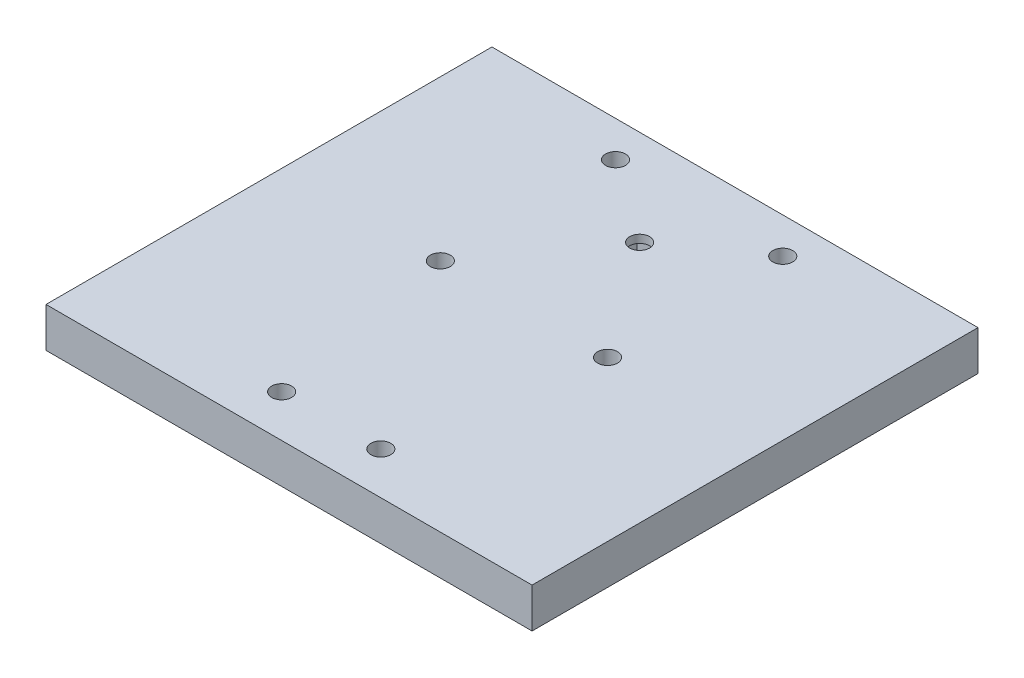
SolidWorks part; units mm, degrees
ref_plane "Front Plane" through (0, 0, 0) normal (0, 0, 1) x (1, 0, 0)
ref_plane "Top Plane" through (0, 0, 0) normal (0, 1, 0) x (1, 0, 0)
ref_plane "Right Plane" through (0, 0, 0) normal (1, 0, 0) x (0, 0, -1)
sketch "Sketch2" plane through (0, 0, 0) normal (0, 1, 0) x (1, 0, 0)
  line L1 (61.04, -67.5) -> (-61.04, -67.5)
  line L2 (61.04, -67.5) -> (61.04, 37.5)
  line L4 (-61.04, -67.5) -> (-61.04, 37.5)
  line L7 (-61.04, 37.5) -> (-61.04, 44.5)
  line L8 (-61.04, 44.5) -> (61.04, 44.5)
  line L9 (61.04, 44.5) -> (61.04, 37.5)
  point P0 (0, 0)
  dimension "D1" = 112
  dimension "D4" = 122.08
extrude "Boss-Extrude1" add sketch "Sketch2" along normal blind 10
sketch "Sketch3" plane through (0, 10, 0) normal (0, 1, 0) x (1, 0, 0)
  line L0 (0, -53.9211) -> (0, 63.05) construction
  line L3 (2.5, 63.05) -> (-2.5, 63.05) construction
  line L6 (61.04, 44.5) -> (-61.04, 44.5) construction
  circle A0 centre (-21, 35.5) radius 3
  circle A1 centre (21, 35.5) radius 3
  circle A2 centre (-21, -8.5) radius 3
  circle A3 centre (21, -8.5) radius 3
  dimension "D1" = 6
  dimension "D2" = 6
  dimension "D3" = 6
  dimension "D4" = 6
  dimension "D5" = 42
  dimension "D7" = 44
  dimension "D8" = 9
  dimension "D6" = 21
hole_wizard "M6 Tapped Hole2" positions "Sketch5" profile "Sketch6" tap size "M6" standard "KS" end condition through all
sketch "Sketch5" plane through (0, 10, 0) normal (0, 1, 0) x (1, 0, 0)
  point P0 (-21, -8.5)
  point P3 (21, -8.5)
  point P6 (21, 35.5)
  point P9 (-21, 35.5)
sketch "Sketch6" plane through (-21, 10, 8.5) normal (1, 0, 0) x (0, 0, 1)
  line L0 (0, 0) -> (0, 10)
  line L1 (0, 10) -> (2.5, 10)
  line L2 (2.5, 10) -> (2.5, 0)
  line L5 (2.5, 0) -> (0, 0)
  line L11 (0, -6.35) -> (0, 107.95) construction
  dimension "Thru Tap Drill Dia." = 5
  dimension "Thru Tap Drill Depth" = 10
cosmetic thread "Hole Thread1" parameters "D2"=6
cosmetic thread "Hole Thread2" parameters "D2"=6
cosmetic thread "Hole Thread3" parameters "D2"=6
cosmetic thread "Hole Thread4" parameters "D2"=6
sketch "Sketch11" plane through (0, 10, 0) normal (0, 1, 0) x (1, 0, 0)
  line L0 (-12.45, -48.4) -> (-12.45, -65.4) construction
  line L1 (-16.95, -56.9) -> (-7.95, -56.9) construction
  line L2 (-16.95, -52.9) -> (-16.95, -60.9) construction
  line L3 (-7.95, -60.9) -> (-7.95, -52.9) construction
  line L4 (7.95, -56.9) -> (16.95, -56.9) construction
  line L5 (7.95, -52.9) -> (7.95, -60.9) construction
  line L6 (16.95, -60.9) -> (16.95, -52.9) construction
  line L7 (12.45, -48.4) -> (12.45, -65.4) construction
  arc A0 (-7.95, -52.9) -> (-16.95, -52.9) centre (-12.45, -52.9) ccw construction
  arc A1 (-16.95, -60.9) -> (-7.95, -60.9) centre (-12.45, -60.9) ccw construction
  arc A2 (16.95, -52.9) -> (7.95, -52.9) centre (12.45, -52.9) ccw construction
  arc A3 (7.95, -60.9) -> (16.95, -60.9) centre (12.45, -60.9) ccw construction
  circle A4 centre (12.45, -56.9) radius 3
  circle A5 centre (-12.45, -56.9) radius 3
  dimension "D1" = 6
  dimension "D2" = 6
hole_wizard "M6 Tapped Hole5" positions "Sketch12" profile "Sketch13" tap size "M6" standard "DIN" end condition through all
sketch "Sketch12" plane through (0, 10, 0) normal (0, 1, 0) x (1, 0, 0)
  point P0 (-12.45, -56.9)
  point P3 (12.45, -56.9)
sketch "Sketch13" plane through (-12.45, 10, 56.9) normal (1, 0, 0) x (0, 0, 1)
  line L0 (0, 0) -> (0, 10)
  line L1 (0, 10) -> (2.5, 10)
  line L2 (2.5, 10) -> (2.5, 0)
  line L5 (2.5, 0) -> (0, 0)
  line L11 (0, -6.35) -> (0, 107.95) construction
  dimension "Thru Tap Drill Dia." = 5
  dimension "Thru Tap Drill Depth" = 10
cosmetic thread "Hole Thread13" parameters "D2"=6
cosmetic thread "Hole Thread14" parameters "D2"=6
sketch "Sketch14" plane through (0, 0, 0) normal (0, -1, 0) x (-1, 0, 0)
  line L0 (0, -53.9211) -> (0, 63.05) construction
  line L1 (-7.7364, 27.5697) -> (7.7364, 27.5697)
  line L2 (-7.7364, 27.5697) -> (-7.7364, 13.5303)
  line L3 (-7.7364, 13.5303) -> (7.7364, 13.5303)
  line L4 (7.7364, 27.5697) -> (7.7364, 13.5303)
  point P0 (0, 20.55)
extrude "Cut-Extrude1" cut sketch "Sketch14" against normal blind 8
hole_wizard "M6 Tapped Hole7" positions "Sketch17" profile "Sketch18" tap size "M6" standard "DIN" end condition through all
sketch "Sketch17" plane through (0, 0, 0) normal (0, -1, 0) x (-1, 0, 0)
  line L0 (0, -53.9211) -> (0, 63.05) construction
  point P0 (0, 20.55)
sketch "Sketch18" plane through (0, 0, -20.55) normal (1, 0, 0) x (0, 0, -1)
  line L0 (0, 0) -> (0, 10)
  line L1 (0, 10) -> (2.5, 10)
  line L2 (2.5, 10) -> (2.5, 0)
  line L5 (2.5, 0) -> (0, 0)
  line L11 (0, -6.35) -> (0, 107.95) construction
  dimension "Thru Tap Drill Dia." = 5
  dimension "Thru Tap Drill Depth" = 10
cosmetic thread "Hole Thread16" parameters "D2"=6
